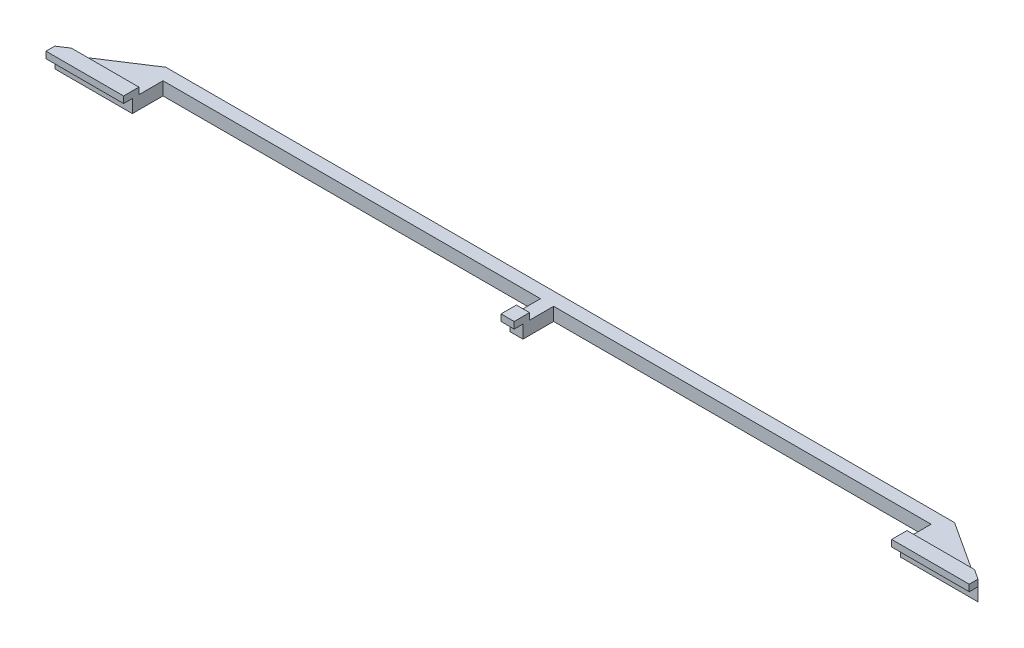
SolidWorks part; units mm, degrees
ref_plane "Front Plane" through (0, 0, 0) normal (0, 0, 1) x (1, 0, 0)
ref_plane "Top Plane" through (0, 0, 0) normal (0, 1, 0) x (1, 0, 0)
ref_plane "Right Plane" through (0, 0, 0) normal (1, 0, 0) x (0, 0, -1)
sketch "Sketch1" plane through (0, 0, 0) normal (0, 1, 0) x (1, 0, 0)
  line L1 (450, 15) -> (-450, 15)
  line L2 (450, 15) -> (450, -15)
  line L3 (450, -15) -> (-450, -15)
  line L4 (-450, 15) -> (-450, -15)
  line L5 (450, 15) -> (-450, -15) construction
  line L6 (450, -15) -> (-450, 15) construction
  point P0 (0, 0)
  dimension "D1" = 30
  dimension "D2" = 900
extrude "Boss-Extrude1" add sketch "Sketch1" along normal blind 30
sketch "Sketch2" plane through (0, 30, 0) normal (0, 1, 0) x (1, 0, 0)
  line L0 (-450, 15) -> (-603.4968, -85)
  line L1 (-603.4968, -85) -> (-426.4491, -85)
  line L2 (-426.4491, -85) -> (-426.4491, 15)
  line L3 (450, 15) -> (-450, 15) construction
  line L4 (-426.4491, 15) -> (-450, 15)
  line L6 (450, 15) -> (450, -85)
  line L7 (450, -85) -> (435, -85)
  line L8 (435, -85) -> (435, 15)
  line L9 (435, 15) -> (450, 15)
  dimension "D1" = 15
  dimension "D2" = 100
  dimension "D3" = 23.5509
extrude "Boss-Extrude2" add sketch "Sketch2" against normal blind 30
sketch "Sketch3" plane through (0, 30, 0) normal (0, 1, 0) x (1, 0, 0)
  line L0 (-603.4968, -85) -> (-580.4723, -70)
  line L1 (-450, 15) -> (-603.4968, -85) construction
  line L2 (-580.4723, -70) -> (-426.4491, -70)
  line L3 (-426.4491, -85) -> (-426.4491, -15) construction
  line L4 (-426.4491, -70) -> (-426.4491, -85)
  line L5 (-426.4491, -85) -> (-603.4968, -85)
  line L6 (450, -85) -> (435, -85)
  line L7 (435, -15) -> (435, -85) construction
  line L8 (435, -85) -> (435, -70)
  line L9 (435, -70) -> (450, -70)
  line L10 (450, -85) -> (450, 15) construction
  line L11 (450, -70) -> (450, -85)
  dimension "D1" = 15
extrude "Boss-Extrude3" add sketch "Sketch3" along normal blind 15
sketch "Sketch4" plane through (0, 0, 85) normal (0, 0, 1) x (1, 0, 0)
  line L0 (-603.4968, 45) -> (-426.4491, 45)
  line L1 (-426.4491, 45) -> (-426.4491, 30)
  line L3 (-426.4491, 30) -> (-603.4968, 30)
  line L5 (-603.4968, 30) -> (-603.4968, 45)
  line L6 (435, 45) -> (450, 45)
  line L7 (450, 45) -> (450, 30)
  line L8 (450, 30) -> (435, 29.8945)
  line L9 (435, 0) -> (435, 45) construction
  line L10 (435, 29.8945) -> (435, 45)
  dimension "D1" = 15
  dimension "D2" = 15
extrude "Boss-Extrude4" add sketch "Sketch4" along normal blind 20
mirror "Mirror1" about plane through (450, 30, -15) normal (-1, 0, 0) of bodies 104
